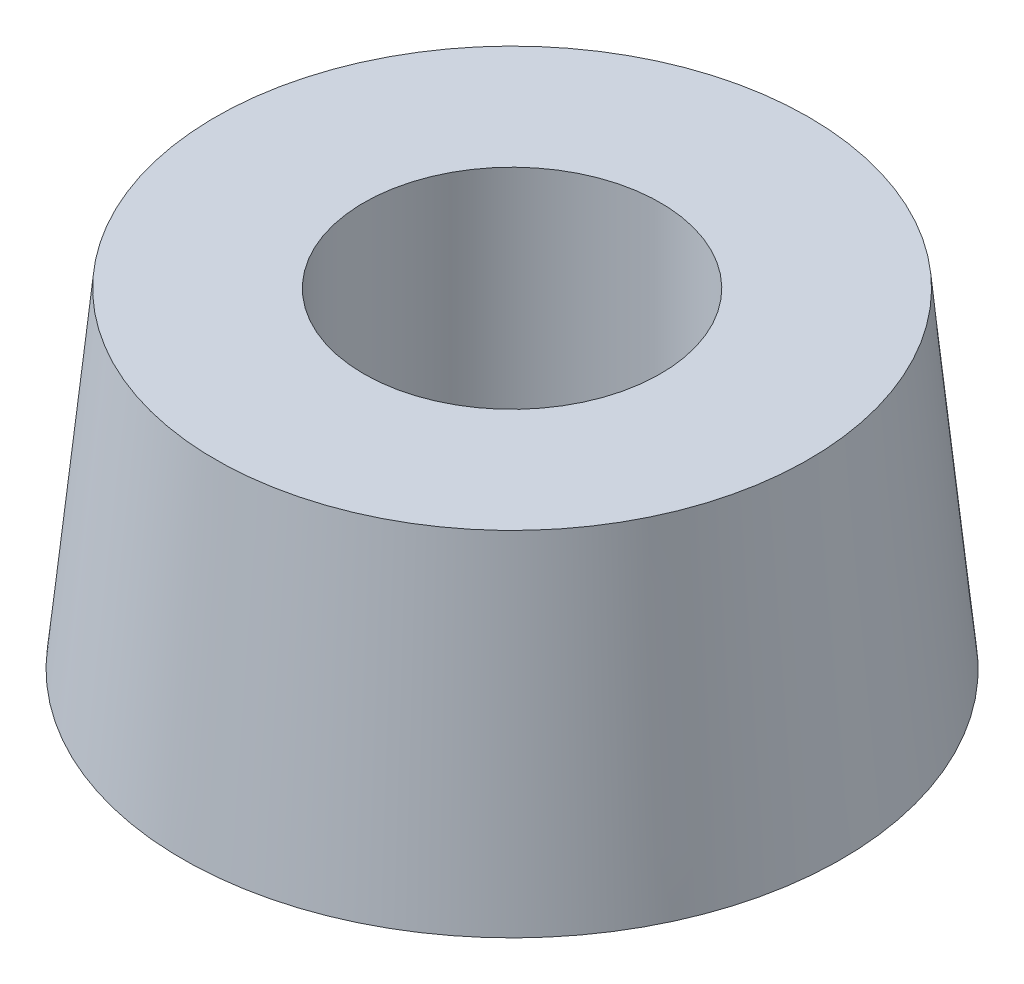
SolidWorks part; units mm, degrees
ref_plane "Płaszczyzna przednia" through (0, 0, 0) normal (0, 0, 1) x (1, 0, 0)
ref_plane "Płaszczyzna górna" through (0, 0, 0) normal (0, 1, 0) x (1, 0, 0)
ref_plane "Płaszczyzna prawa" through (0, 0, 0) normal (1, 0, 0) x (0, 0, -1)
sketch "Szkic5" plane through (0, 0, 0) normal (1, 0, 0) x (0, 0, -1)
  line L0 (0, 0) -> (0, 16.5967) construction
  line L1 (0, 10) -> (-9, 10)
  line L2 (-9, 10) -> (-10, 0)
  line L3 (-10, 0) -> (0, 0)
  line L4 (0, 0) -> (0, 10)
  dimension "D1" = 18
  dimension "D2" = 20
  dimension "D3" = 10
revolve "Obrót1" add sketch "Szkic5" angle 360 about L0
sketch "Szkic6" plane through (0, 10, 0) normal (0, 1, 0) x (1, 0, 0)
  circle A0 centre (0, 0) radius 4.5
  dimension "D1" = 9
extrude "Wytnij-wyciągnięcie1" cut sketch "Szkic6" against normal blind 6.5
sketch "Szkic7" plane through (0, 3.5, 0) normal (0, 1, 0) x (1, 0, 0)
  circle A0 centre (0, 0) radius 2.5
  dimension "D1" = 5
extrude "Wytnij-wyciągnięcie2" cut sketch "Szkic7" against normal up to next and the other way through all
